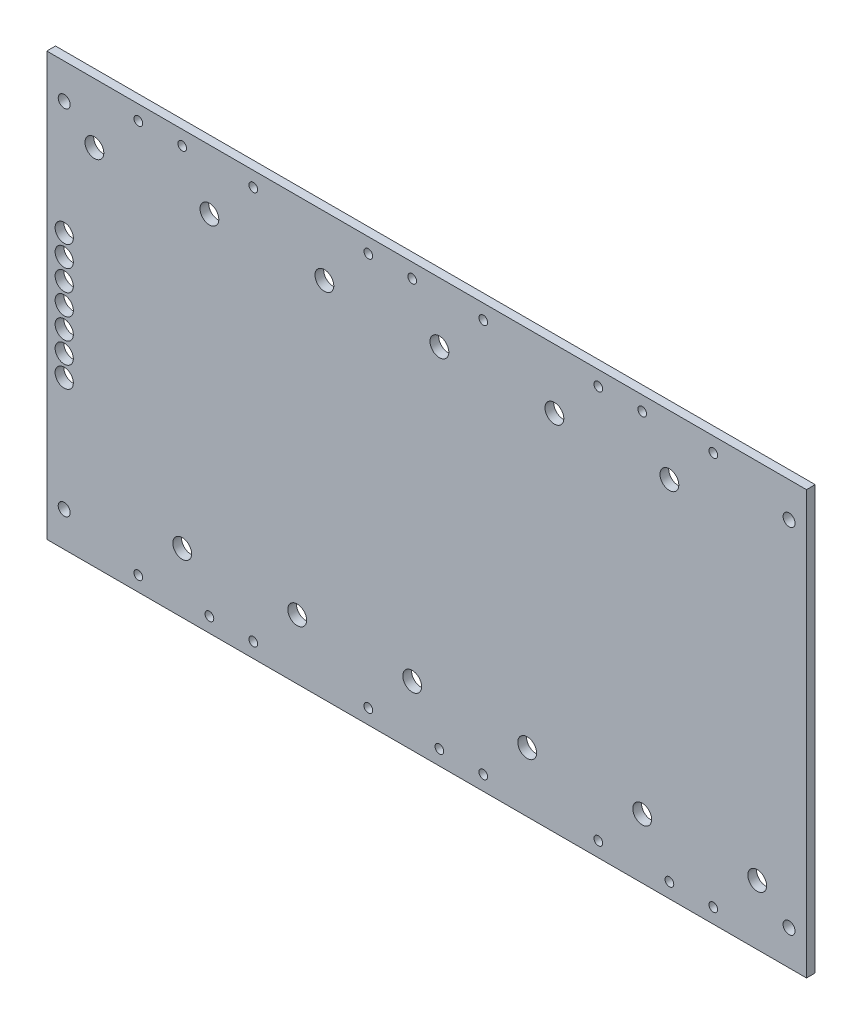
SolidWorks part; units mm, degrees
ref_plane "Front Plane" through (0, 0, 0) normal (0, 0, 1) x (1, 0, 0)
ref_plane "Top Plane" through (0, 0, 0) normal (0, 1, 0) x (1, 0, 0)
ref_plane "Right Plane" through (0, 0, 0) normal (1, 0, 0) x (0, 0, -1)
sketch "Sketch1" plane through (0, 0, 0) normal (0, 0, 1) x (1, 0, 0)
  line L0 (20.955, 77.0636) -> (20.955, 0) construction
  line L1 (0, 0) -> (132.08, 0)
  line L2 (0, 0) -> (0, 77.0636) construction
  line L3 (0, 77.0636) -> (132.08, 77.0636)
  line L4 (132.08, 77.0636) -> (132.08, 0)
  line L5 (20.6502, 77.0636) -> (20.6502, 0) construction
  line L6 (10.3251, 74.3712) -> (0, 74.3712) construction
  line L7 (10.3251, 74.3712) -> (20.6502, 74.3712) construction
  line L8 (10.3251, 2.6924) -> (10.3251, 0) construction
  line L9 (10.3251, 74.3712) -> (10.3251, 77.0636) construction
  line L10 (18.3261, 66.1543) -> (20.6502, 66.1543) construction
  line L11 (2.3241, 66.1543) -> (0, 66.1543) construction
  line L12 (18.3261, 10.9093) -> (20.6502, 10.9093) construction
  line L13 (41.6052, 77.0636) -> (41.6052, 0) construction
  line L14 (18.3261, 66.1543) -> (18.3261, 77.0636) construction
  line L15 (18.3261, 10.9093) -> (18.3261, 0) construction
  line L16 (20.955, 66.1543) -> (23.2791, 66.1543) construction
  line L17 (41.6052, 66.1543) -> (36.2579, 66.1543) construction
  line L18 (41.6052, 74.3712) -> (20.955, 74.3712) construction
  line L19 (31.2801, 74.3712) -> (31.2801, 77.0636) construction
  line L20 (31.2801, 0) -> (31.2801, 2.6924) construction
  line L21 (0, 77.0636) -> (-6.35, 77.0636)
  line L22 (-6.35, 77.0636) -> (-6.35, 0)
  line L23 (-6.35, 0) -> (0, 0)
  line L24 (41.6052, 10.9093) -> (39.2811, 10.9093) construction
  line L25 (41.6052, 2.6924) -> (31.2801, 2.6924) construction
  line L26 (83.5152, 77.0636) -> (83.5152, 0) construction
  line L27 (-3.175, 70.7136) -> (-3.175, 77.0636) construction
  line L28 (-3.175, 6.35) -> (-3.175, 0) construction
  line L29 (62.865, 77.0636) -> (62.865, 0) construction
  line L30 (62.5602, 77.0636) -> (62.5602, 0) construction
  line L31 (41.91, 0) -> (41.91, 77.0636) construction
  line L32 (125.4252, 77.0636) -> (125.4252, 0) construction
  line L33 (104.775, 77.0636) -> (104.775, 0) construction
  line L34 (104.4702, 77.0636) -> (104.4702, 0) construction
  line L35 (83.82, 0) -> (83.82, 77.0636) construction
  line L36 (41.6052, 77.0636) -> (83.5152, 77.0636) construction
  line L37 (128.905, 77.0636) -> (128.905, 70.7136) construction
  line L38 (128.905, 0) -> (128.905, 6.35) construction
  line L39 (20.955, 2.6924) -> (23.2791, 2.6924) construction
  line L40 (23.2791, 2.6924) -> (65.1891, 2.6924) construction
  line L41 (94.1451, 74.3712) -> (115.1001, 74.3712) construction
  line L42 (-3.175, 38.5318) -> (-6.35, 38.5318) construction
  line L43 (-3.175, 38.5318) -> (-3.175, 42.3418) construction
  circle A0 centre (10.3251, 74.3712) radius 0.7937
  circle A1 centre (10.3251, 2.6924) radius 0.7937
  circle A2 centre (2.3241, 66.1543) radius 1.7145
  circle A3 centre (18.3261, 74.4347) radius 0.7937
  circle A4 centre (18.3261, 10.9093) radius 1.7145
  circle A5 centre (23.2791, 66.1543) radius 1.7145
  circle A6 centre (31.2801, 74.3712) radius 0.7937
  circle A7 centre (31.2801, 2.6924) radius 0.7937
  circle A8 centre (39.2811, 10.9093) radius 1.7145
  circle A9 centre (31.2801, 2.6924) radius 0.7937
  circle A10 centre (65.1891, 66.1543) radius 1.7145
  circle A11 centre (73.1901, 2.6924) radius 0.7937
  circle A12 centre (73.1901, 2.6924) radius 0.7937
  circle A13 centre (81.1911, 10.9093) radius 1.7145
  circle A14 centre (73.1901, 74.3712) radius 0.7937
  circle A15 centre (65.1891, 2.6924) radius 0.7937
  circle A16 centre (52.2351, 74.3712) radius 0.7937
  circle A17 centre (44.2341, 66.1543) radius 1.7145
  circle A18 centre (-3.175, 70.7136) radius 1.0922
  circle A19 centre (-3.175, 6.35) radius 1.0922
  circle A20 centre (60.2361, 10.9093) radius 1.7145
  circle A21 centre (52.2351, 2.6924) radius 0.7937
  circle A22 centre (107.0991, 66.1543) radius 1.7145
  circle A23 centre (115.1001, 2.6924) radius 0.7937
  circle A24 centre (115.1001, 2.6924) radius 0.7937
  circle A25 centre (123.1011, 10.9093) radius 1.7145
  circle A26 centre (60.2361, 74.4347) radius 0.7937
  circle A27 centre (102.1461, 74.4347) radius 0.7937
  circle A28 centre (94.1451, 74.3712) radius 0.7937
  circle A29 centre (86.1441, 66.1543) radius 1.7145
  circle A30 centre (102.1461, 10.9093) radius 1.7145
  circle A31 centre (94.1451, 2.6924) radius 0.7937
  circle A32 centre (128.905, 70.7136) radius 1.0922
  circle A33 centre (128.905, 6.35) radius 1.0922
  circle A34 centre (23.2791, 2.6924) radius 0.7937
  circle A35 centre (60.2361, 74.4347) radius 0.7937 [skipped]
  circle A36 centre (115.1001, 74.3712) radius 0.7937 [skipped]
  circle A37 centre (107.0991, 2.6924) radius 0.7937
  circle A38 centre (102.1461, 74.4347) radius 0.7937
  circle A39 centre (115.1001, 74.3712) radius 0.7937
  circle A40 centre (-3.175, 38.5318) radius 1.6593
  circle A41 centre (-3.175, 42.3418) radius 1.6593
  circle A42 centre (-3.175, 46.1518) radius 1.6593
  circle A43 centre (-3.175, 49.9618) radius 1.6593
  circle A44 centre (-3.175, 38.5318) radius 1.6593
  circle A45 centre (-3.175, 42.3418) radius 1.6593
  circle A46 centre (-3.175, 46.1518) radius 1.6593
  circle A47 centre (-3.175, 34.7218) radius 1.6593
  circle A48 centre (-3.175, 38.5318) radius 1.6593
  circle A49 centre (-3.175, 42.3418) radius 1.6593
  circle A50 centre (-3.175, 30.9118) radius 1.6593
  circle A51 centre (-3.175, 34.7218) radius 1.6593
  circle A52 centre (-3.175, 38.5318) radius 1.6593
  circle A53 centre (-3.175, 34.7218) radius 1.6593
  circle A54 centre (-3.175, 30.9118) radius 1.6593
  circle A55 centre (-3.175, 27.1018) radius 1.6593
  dimension "D6" = 1.5875
  dimension "D7" = 3.429
  dimension "D13" = 2.1844
  dimension "D15" = 20.6502
  dimension "D11" = 1.5875
  dimension "D16" = 3
  dimension "D18" = 41.91
  dimension "D24" = 3.3186
  dimension "D1" = 77.0636
  dimension "D2" = 132.08
  dimension "D3" = 20.6502
  dimension "D4" = 20.955
  dimension "D5" = 71.6788
  dimension "D8" = 16.002
  dimension "D9" = 55.245
  dimension "D10" = 8.2804
  dimension "D12" = 6.35
  dimension "D14" = 6.35
  dimension "D17" = 3
  dimension "D19" = 71.6788
  dimension "D20" = 3.175
  dimension "D21" = 41.91
  dimension "D23" = 20.955
  dimension "D27" = 3.81
  dimension "D22" = 2
  dimension "D25" = 4
  dimension "D26" = 4
extrude "Boss-Extrude1" add sketch "Sketch1" along normal blind 1.5875
